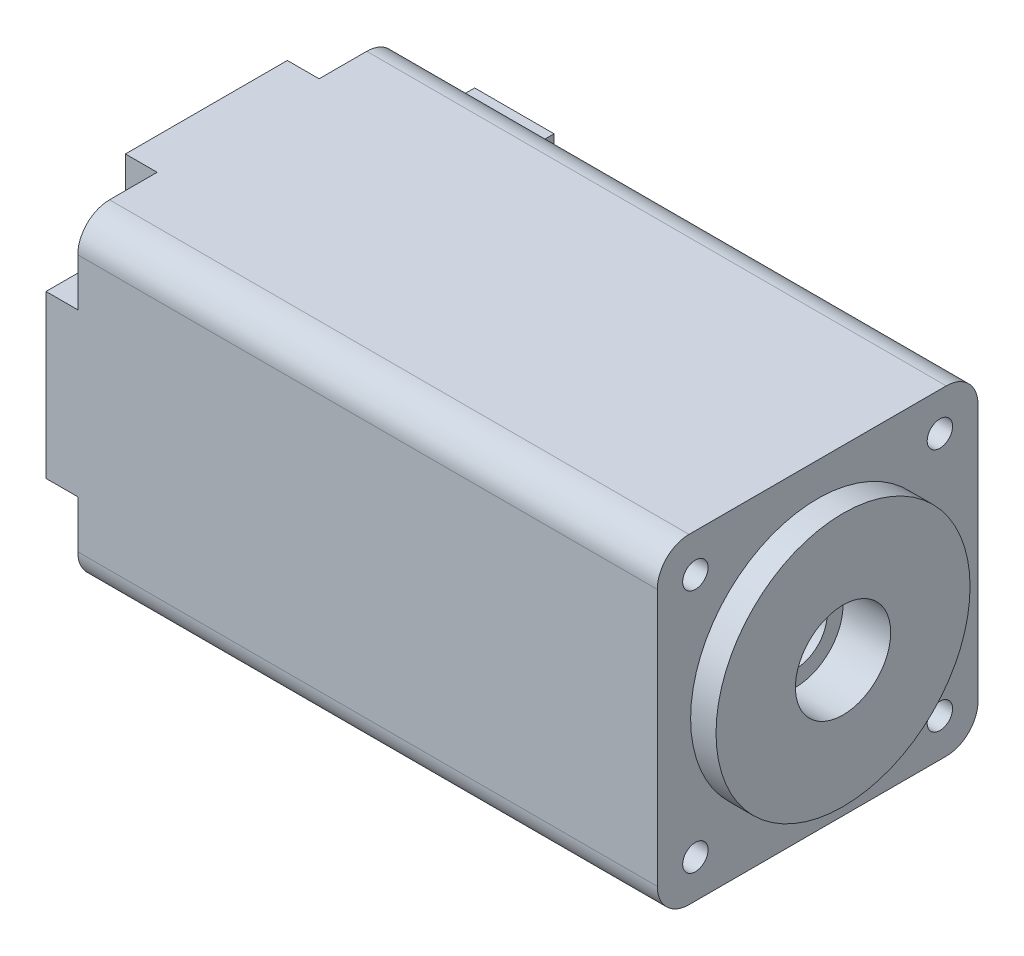
SolidWorks part; units mm, degrees
material "3.1355 (EN-AW 2024)"
ref_plane "Спереди" through (0, 0, 0) normal (0, 0, 1) x (1, 0, 0)
ref_plane "Сверху" through (0, 0, 0) normal (0, 1, 0) x (1, 0, 0)
ref_plane "Справа" through (0, 0, 0) normal (1, 0, 0) x (0, 0, -1)
sketch "Эскиз1" plane through (0, 0, 0) normal (1, 0, 0) x (0, 0, -1)
  line L1 (0, 0) -> (20.2, 0)
  line L2 (0, 0) -> (0, 20.2)
  line L3 (0, 20.2) -> (20.2, 20.2)
  line L4 (20.2, 0) -> (20.2, 20.2)
  dimension "D1" = 20.2
extrude "Бобышка-Вытянуть1" add sketch "Эскиз1" along normal blind 38.5
sketch "Эскиз2" plane through (38.5, 0, 0) normal (1, 0, 0) x (0, 0, -1)
  line L0 (10.1, 20.2) -> (10.1, 0) construction
  line L1 (20.2, 20.2) -> (0, 20.2) construction
  line L2 (0, 0) -> (20.2, 0) construction
  circle A0 centre (10.1, 10.1) radius 8
  dimension "D1" = 16
extrude "Бобышка-Вытянуть2" add sketch "Эскиз2" along normal blind 1.6
sketch "Эскиз3" plane through (0, 0, 0) normal (-1, 0, 0) x (0, 0, 1)
  line L0 (-10.1, 20.2) -> (-10.1, 0) construction
  line L1 (-20.2, 20.2) -> (0, 20.2) construction
  line L2 (0, 0) -> (-20.2, 0) construction
  line L3 (-20.2, 10.1) -> (0, 10.1) construction
  line L4 (-20.2, 0) -> (-20.2, 20.2) construction
  line L5 (0, 20.2) -> (0, 0) construction
  line L6 (-5, 20.2) -> (-5, 18.2)
  line L7 (-20.2, 20.2) -> (-15.2, 20.2)
  line L8 (-20.2, 20.2) -> (-20.2, 15.2)
  line L9 (-20.2, 15.2) -> (-18.2, 15.2)
  line L10 (-15.2, 20.2) -> (-15.2, 18.2)
  line L11 (0, 15.2) -> (-2, 15.2)
  line L12 (0, 20.2) -> (0, 15.2)
  line L13 (0, 20.2) -> (-5, 20.2)
  line L14 (0, 0) -> (-5, 0)
  line L15 (0, 0) -> (0, 5)
  line L16 (0, 5) -> (-2, 5)
  line L17 (-15.2, 0) -> (-15.2, 2)
  line L18 (-20.2, 5) -> (-18.2, 5)
  line L19 (-20.2, 0) -> (-20.2, 5)
  line L20 (-20.2, 0) -> (-15.2, 0)
  line L21 (-5, 0) -> (-5, 2)
  arc A0 (-18.2, 15.2) -> (-15.2, 18.2) centre (-18.2, 18.2) ccw
  arc A1 (-2, 15.2) -> (-5, 18.2) centre (-2, 18.2) cw
  arc A2 (-2, 5) -> (-5, 2) centre (-2, 2) ccw
  arc A3 (-18.2, 5) -> (-15.2, 2) centre (-18.2, 2) cw
  dimension "D2" = 3
  dimension "D1" = 5
extrude "Вырез-Вытянуть1" cut sketch "Эскиз3" against normal blind 2
sketch "Эскиз4" plane through (2, 0, 0) normal (-1, 0, 0) x (0, 0, 1)
  line L0 (-10.1, 20.2) -> (-10.1, 0) construction
  line L1 (-15.2, 20.2) -> (-5, 20.2) construction
  line L2 (-5, 0) -> (-15.2, 0) construction
  line L4 (-20.2, 5) -> (-20.2, 15.2) construction
  line L5 (-20.2, 10.1) -> (0, 10.1) construction
  line L6 (0, 15.2) -> (0, 5) construction
  line L7 (-17.8, 17.8) -> (-2.4, 17.8) construction
  line L8 (-17.8, 17.8) -> (-17.8, 2.4) construction
  line L9 (-17.8, 2.4) -> (-2.4, 2.4) construction
  line L10 (-2.4, 17.8) -> (-2.4, 2.4) construction
  line L11 (-17.8, 17.8) -> (-2.4, 2.4) construction
  line L12 (-17.8, 2.4) -> (-2.4, 17.8) construction
  point P6 (-10.1, 10.1)
  dimension "D1" = 15.4
hole_wizard "Отверстие обработанное метчиком M2x0.41" positions "Эскиз6" profile "Эскиз5" tap size "M2x0.4" standard "Ansi Metric" end condition through all
sketch "Эскиз6" plane through (2, 0, 0) normal (-1, 0, 0) x (0, 0, 1)
  point P0 (-17.8, 17.8)
  point P3 (-2.4, 17.8)
  point P6 (-2.4, 2.4)
  point P9 (-17.8, 2.4)
sketch "Эскиз5" plane through (2, 17.8, -17.8) normal (0, 1, 0) x (0, 0, 1)
  line L0 (0, 0) -> (0, 38.1)
  line L1 (0, 38.1) -> (0.8, 38.1)
  line L2 (0.8, 38.1) -> (0.8, 0)
  line L5 (0.8, 0) -> (0, 0)
  line L11 (0, -6.35) -> (0, 107.95) construction
  dimension "Диаметр проходного сверла" = 1.6
  dimension "Глубина проходного сверла" = 38.1
cosmetic thread "Отверстие резьбы1" parameters "D2"=2
cosmetic thread "Отверстие резьбы2" parameters "D2"=2
cosmetic thread "Отверстие резьбы3" parameters "D2"=2
cosmetic thread "Отверстие резьбы4" parameters "D2"=2
fillet "Скругление1" radius 2 4 edges at (20.25, 0, -20.2) (20.25, 0, 0) (20.25, 20.2, 0) (20.25, 20.2, -20.2)
sketch "Эскиз7" plane through (40.1, 0, 0) normal (1, 0, 0) x (0, 0, -1)
  circle A0 centre (10.1, 10.1) radius 2
  dimension "D1" = 4
extrude "Вырез-Вытянуть2" cut sketch "Эскиз7" against normal through all
sketch "Эскиз8" plane through (0, 0, 0) normal (-1, 0, 0) x (0, 0, 1)
  circle A0 centre (-10.1, 10.1) radius 2.65
  dimension "D1" = 5.3
extrude "Вырез-Вытянуть3" cut sketch "Эскиз8" against normal blind 5.5
sketch "Эскиз9" plane through (40.1, 0, 0) normal (1, 0, 0) x (0, 0, -1)
  circle A0 centre (10.1, 10.1) radius 3
  dimension "D1" = 6
extrude "Вырез-Вытянуть4" cut sketch "Эскиз9" against normal blind 3
sketch "Эскиз10" plane through (0, 0, -20.2) normal (0, 0, -1) x (-1, 0, 0)
  line L0 (-2, 10.1) -> (-38.5, 10.1) construction
  line L1 (-8.3, 4.1) -> (-3.3, 4.1)
  line L2 (-8.3, 4.1) -> (-8.3, 16.1)
  line L3 (-8.3, 16.1) -> (-3.3, 16.1)
  line L4 (-3.3, 4.1) -> (-3.3, 16.1)
  line L5 (-8.3, 4.1) -> (-3.3, 16.1) construction
  line L6 (-8.3, 16.1) -> (-3.3, 4.1) construction
  line L7 (-38.5, 2) -> (-38.5, 18.2) construction
  line L8 (0, 5) -> (0, 15.2) construction
  point P0 (-5.8, 10.1)
  dimension "D1" = 5
  dimension "D2" = 12
  dimension "D3" = 3.3
extrude "Бобышка-Вытянуть3" add sketch "Эскиз10" along normal blind 3.5
